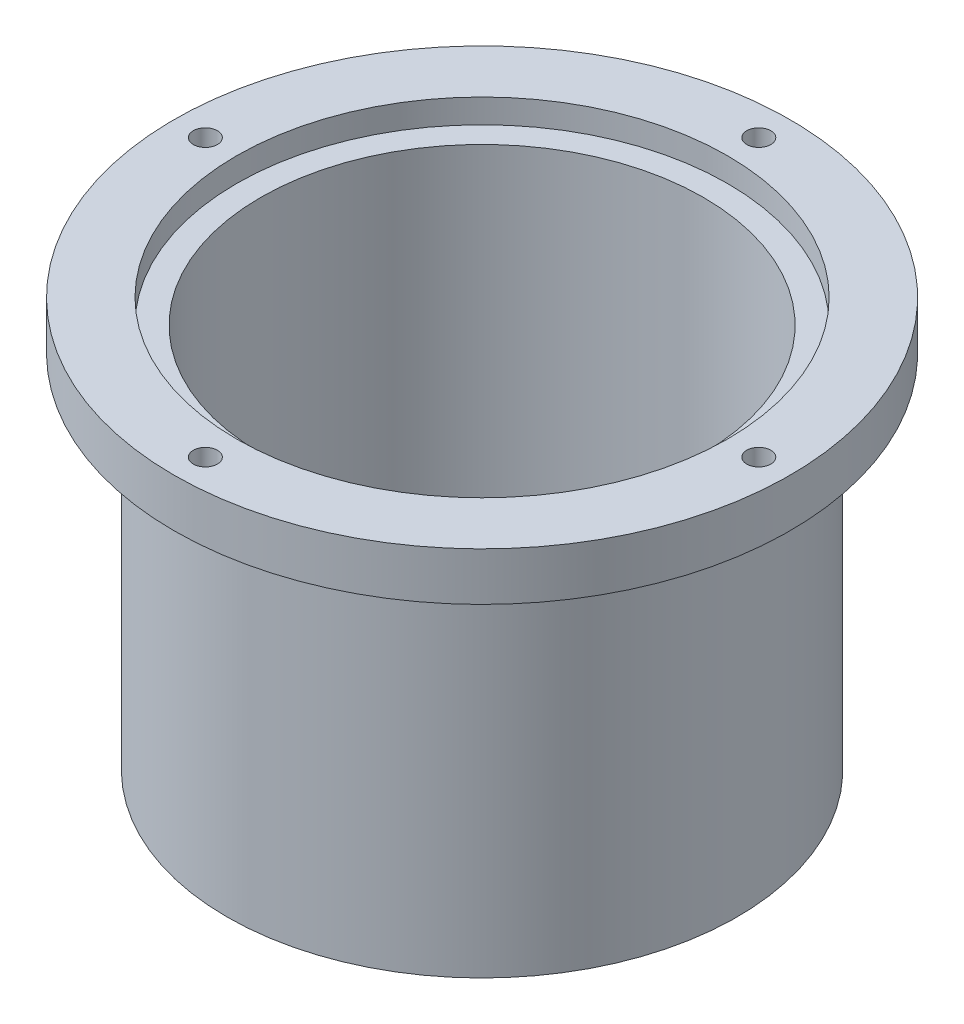
SolidWorks part; units mm, degrees
material "PE High Density"
ref_plane "Front Plane" through (0, 0, 0) normal (0, 0, 1) x (1, 0, 0)
ref_plane "Top Plane" through (0, 0, 0) normal (0, 1, 0) x (1, 0, 0)
ref_plane "Right Plane" through (0, 0, 0) normal (1, 0, 0) x (0, 0, -1)
sketch "Sketch1" plane through (0, 0, 0) normal (0, 1, 0) x (1, 0, 0)
  circle A0 centre (0, 0) radius 53
extrude "Boss-Extrude1" add sketch "Sketch1" along normal blind 75
sketch "Sketch2" plane through (0, 75, 0) normal (0, 1, 0) x (1, 0, 0)
  circle A0 centre (0, 0) radius 64
extrude "Boss-Extrude2" add sketch "Sketch2" along normal blind 10
sketch "Sketch3" plane through (0, 85, 0) normal (0, 1, 0) x (1, 0, 0)
  circle A0 centre (0, 0) radius 51
extrude "Cut-Extrude1" cut sketch "Sketch3" against normal blind 5
sketch "Sketch5" plane through (0, 80, 0) normal (0, 1, 0) x (1, 0, 0)
  circle A0 centre (0, 0) radius 46
extrude "Cut-Extrude2" cut sketch "Sketch5" against normal blind 66
sketch "Sketch6" plane through (0, 85, 0) normal (0, 1, 0) x (1, 0, 0)
  circle A0 centre (-57.5, 0) radius 2.5
  circle A1 centre (0, 57.5) radius 2.5
  circle A2 centre (57.5, 0) radius 2.5
  circle A3 centre (0, -57.5) radius 2.5
  point P12 (0, 0)
  dimension "D1" = 4
extrude "Cut-Extrude3" cut sketch "Sketch6" against normal blind 66
